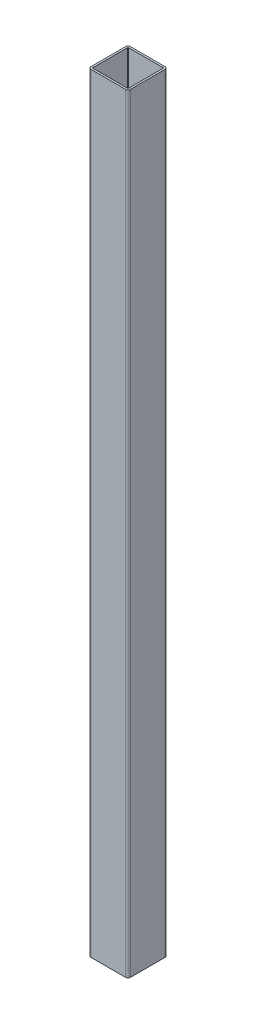
SolidWorks part; units mm, degrees
ref_plane "Front Plane" through (0, 0, 0) normal (0, 0, 1) x (1, 0, 0)
ref_plane "Top Plane" through (0, 0, 0) normal (0, 1, 0) x (1, 0, 0)
ref_plane "Right Plane" through (0, 0, 0) normal (1, 0, 0) x (0, 0, -1)
sketch "Sketch1" plane through (0, 0, 0) normal (0, 1, 0) x (1, 0, 0)
  line L0 (1.6, 2) -> (1.6, 31.3333)
  line L1 (2, 0) -> (31.3333, 0)
  line L2 (0, 2) -> (0, 31.3333)
  line L3 (2, 33.3333) -> (31.3333, 33.3333)
  line L4 (33.3333, 2) -> (33.3333, 31.3333)
  line L5 (2, 31.7333) -> (31.3333, 31.7333)
  line L6 (31.7333, 2) -> (31.7333, 31.3333)
  line L7 (2, 1.6) -> (31.3333, 1.6)
  arc A0 (31.3333, 33.3333) -> (33.3333, 31.3333) centre (31.3333, 31.3333) cw
  arc A1 (0, 31.3333) -> (2, 33.3333) centre (2, 31.3333) cw
  arc A2 (31.3333, 0) -> (33.3333, 2) centre (31.3333, 2) ccw
  arc A3 (2, 0) -> (0, 2) centre (2, 2) cw
  arc A4 (1.6, 31.3333) -> (2, 31.7333) centre (2, 31.3333) cw
  arc A5 (31.3333, 31.7333) -> (31.7333, 31.3333) centre (31.3333, 31.3333) cw
  arc A6 (31.3333, 1.6) -> (31.7333, 2) centre (31.3333, 2) ccw
  arc A7 (2, 1.6) -> (1.6, 2) centre (2, 2) cw
  point P9 (0, 33.3333)
  point P14 (0, 0)
  dimension "D2" = 2
  dimension "D3" = 2
  dimension "D1" = 33.3333
  dimension "D4" = 1.6
extrude "Boss-Extrude1" add sketch "Sketch1" along normal blind 650
scale "Scale1" scale about centroid uniform scaling yes scale factor 7.5
